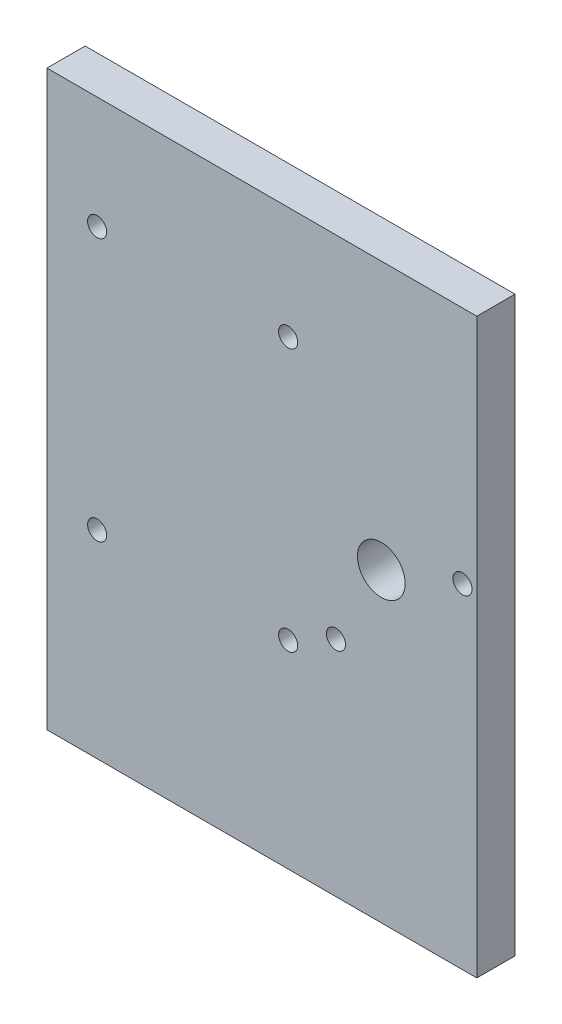
SolidWorks part; units mm, degrees
ref_plane "Front Plane" through (0, 0, 0) normal (0, 0, 1) x (1, 0, 0)
ref_plane "Top Plane" through (0, 0, 0) normal (0, 1, 0) x (1, 0, 0)
ref_plane "Right Plane" through (0, 0, 0) normal (1, 0, 0) x (0, 0, -1)
sketch "Sketch1" plane through (0, 0, 0) normal (0, 0, 1) x (1, 0, 0)
  line L1 (0, 0) -> (90, 0)
  line L2 (0, 0) -> (0, 120)
  line L3 (0, 120) -> (90, 120)
  line L4 (90, 0) -> (90, 120)
  dimension "D1" = 90
  dimension "D2" = 120
extrude "Boss-Extrude1" add sketch "Sketch1" along normal blind 8
sketch "Sketch2" plane through (0, 0, 8) normal (0, 0, 1) x (1, 0, 0)
  line L0 (90, 0) -> (90, 120) construction
  line L1 (90, 120) -> (0, 120) construction
  circle A0 centre (70, 64) radius 5
  dimension "D1" = 20
  dimension "D2" = 56
extrude "Cut-Extrude1" cut sketch "Sketch2" against normal through all
sketch "Sketch3" plane through (0, 0, 8) normal (0, 0, 1) x (1, 0, 0)
  circle A0 centre (87, 70) radius 2
  circle A1 centre (70, 64) radius 5 construction
  circle A2 centre (60.5, 46.7) radius 2
  dimension "D1" = 4
  dimension "D2" = 17
  dimension "D3" = 17.3
  dimension "D4" = 9.5
  dimension "D5" = 6
extrude "Cut-Extrude2" cut sketch "Sketch3" against normal through all
ref_point "Point1"
ref_plane "Plane1" through (0, 111, 0) normal (0, 1, 0) x (-1, 0, 0)
ref_plane "Plane2" through (10, 0, 0) normal (-1, 0, 0) x (0, 0, 1)
sketch "Sketch4" plane through (0, 0, 8) normal (0, 0, 1) x (1, 0, 0)
  circle A0 centre (50.5, 96.5) radius 2
  circle A1 centre (10.5, 96.5) radius 2
  circle A2 centre (50.5, 41.5) radius 2
  circle A3 centre (10.5, 41.5) radius 2
extrude "Cut-Extrude3" cut sketch "Sketch4" against normal through all
